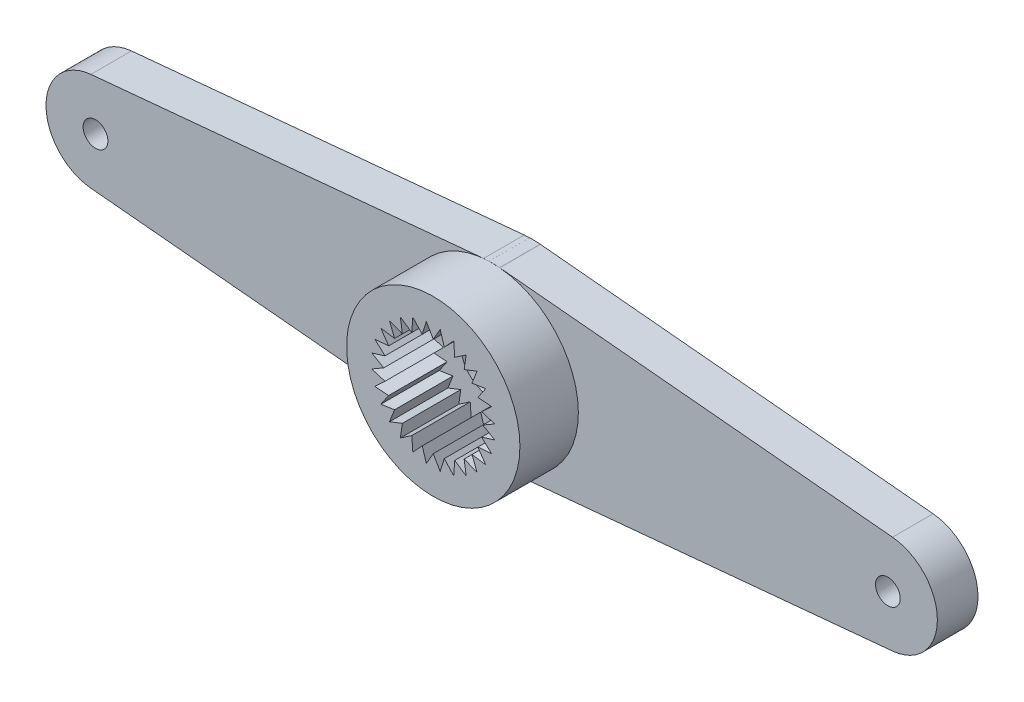
SolidWorks part; units mm, degrees
ref_plane "前视基准面" through (0, 0, 0) normal (0, 0, 1) x (1, 0, 0)
ref_plane "上视基准面" through (0, 0, 0) normal (0, 1, 0) x (1, 0, 0)
ref_plane "右视基准面" through (0, 0, 0) normal (1, 0, 0) x (0, 0, -1)
sketch "草图1" plane through (0, 0, 0) normal (0, 0, 1) x (1, 0, 0)
  circle A0 centre (0, 0) radius 1
extrude "凸台-拉伸1" add sketch "草图1" against normal blind 4.3
sketch "草图2" plane through (0, 0, 0) normal (0, 0, 1) x (1, 0, 0)
  circle A0 centre (0, 0) radius 2
extrude "凸台-拉伸2" add sketch "草图2" along normal blind 1
sketch "草图3" plane through (0, 0, 1) normal (0, 0, 1) x (1, 0, 0)
  line L0 (2.3597, -0.8257) -> (1.8019, -0.8678)
  line L29 (2.4843, -0.2799) -> (1.9499, -0.445)
  line L30 (2.4843, -0.2799) -> (2, 0)
  line L31 (2.3597, -0.8257) -> (1.9499, -0.445)
  line L32 (2.1168, -1.3301) -> (1.5637, -1.247)
  line L33 (2.1168, -1.3301) -> (1.8019, -0.8678)
  line L34 (1.7678, -1.7678) -> (1.247, -1.5637)
  line L35 (1.7678, -1.7678) -> (1.5637, -1.247)
  line L36 (1.3301, -2.1168) -> (0.8678, -1.8019)
  line L37 (1.3301, -2.1168) -> (1.247, -1.5637)
  line L38 (0.8257, -2.3597) -> (0.445, -1.9499)
  line L39 (0.8257, -2.3597) -> (0.8678, -1.8019)
  line L40 (0.2799, -2.4843) -> (0, -2)
  line L41 (0.2799, -2.4843) -> (0.445, -1.9499)
  line L42 (-0.2799, -2.4843) -> (-0.445, -1.9499)
  line L43 (-0.2799, -2.4843) -> (0, -2)
  line L44 (-0.8257, -2.3597) -> (-0.8678, -1.8019)
  line L45 (-0.8257, -2.3597) -> (-0.445, -1.9499)
  line L46 (-1.3301, -2.1168) -> (-1.247, -1.5637)
  line L47 (-1.3301, -2.1168) -> (-0.8678, -1.8019)
  line L48 (-1.7678, -1.7678) -> (-1.5637, -1.247)
  line L49 (-1.7678, -1.7678) -> (-1.247, -1.5637)
  line L50 (-2.1168, -1.3301) -> (-1.8019, -0.8678)
  line L51 (-2.1168, -1.3301) -> (-1.5637, -1.247)
  line L52 (-2.3597, -0.8257) -> (-1.9499, -0.445)
  line L53 (-2.3597, -0.8257) -> (-1.8019, -0.8678)
  line L54 (-2.4843, -0.2799) -> (-2, 0)
  line L55 (-2.4843, -0.2799) -> (-1.9499, -0.445)
  line L56 (-2.4843, 0.2799) -> (-1.9499, 0.445)
  line L57 (-2.4843, 0.2799) -> (-2, 0)
  line L58 (-2.3597, 0.8257) -> (-1.8019, 0.8678)
  line L59 (-2.3597, 0.8257) -> (-1.9499, 0.445)
  line L60 (-2.1168, 1.3301) -> (-1.5637, 1.247)
  line L61 (-2.1168, 1.3301) -> (-1.8019, 0.8678)
  line L62 (-1.7678, 1.7678) -> (-1.247, 1.5637)
  line L63 (-1.7678, 1.7678) -> (-1.5637, 1.247)
  line L64 (-1.3301, 2.1168) -> (-0.8678, 1.8019)
  line L65 (-1.3301, 2.1168) -> (-1.247, 1.5637)
  line L66 (-0.8257, 2.3597) -> (-0.445, 1.9499)
  line L67 (-0.8257, 2.3597) -> (-0.8678, 1.8019)
  line L68 (-0.2799, 2.4843) -> (0, 2)
  line L69 (-0.2799, 2.4843) -> (-0.445, 1.9499)
  line L70 (0.2799, 2.4843) -> (0.445, 1.9499)
  line L71 (0.2799, 2.4843) -> (0, 2)
  line L72 (0.8257, 2.3597) -> (0.8678, 1.8019)
  line L73 (0.8257, 2.3597) -> (0.445, 1.9499)
  line L74 (1.3301, 2.1168) -> (1.247, 1.5637)
  line L75 (1.3301, 2.1168) -> (0.8678, 1.8019)
  line L76 (1.7678, 1.7678) -> (1.5637, 1.247)
  line L77 (1.7678, 1.7678) -> (1.247, 1.5637)
  line L78 (2.1168, 1.3301) -> (1.8019, 0.8678)
  line L79 (2.1168, 1.3301) -> (1.5637, 1.247)
  line L80 (2.3597, 0.8257) -> (1.9499, 0.445)
  line L81 (2.3597, 0.8257) -> (1.8019, 0.8678)
  line L82 (2.4843, 0.2799) -> (2, 0)
  line L83 (2.4843, 0.2799) -> (1.9499, 0.445)
  arc A1 (0.445, -1.9499) -> (0.8678, -1.8019) centre (0, 0) ccw construction
  arc A2 (0, 2) -> (-0.445, 1.9499) centre (0, 0) ccw construction
  arc A3 (-1.5637, -1.247) -> (-1.247, -1.5637) centre (0, 0) ccw construction
  dimension "D1" = 28
extrude "凸台-拉伸3" add sketch "草图3" along normal blind 3.5
sketch "草图6" plane through (0, 0, 0) normal (0, 1, 0) x (1, 0, 0)
  line L0 (0, 0) -> (0, -4.5)
ref_plane "基准面3" through (0, 0, 4.5) normal (0, 0, 1) x (1, 0, 0)
sketch "草图7" plane through (0, 0, 4.5) normal (0, 0, 1) x (1, 0, 0)
  circle A0 centre (0, 0) radius 3.5
extrude "凸台-拉伸4" add sketch "草图7" against normal blind 4 separate body contours A0
combine bodies "组合1" operation type subtract main body 105 bodies to subtract 103
ref_plane "基准面5" through (0, 0, 0.5) normal (0, 0, -1) x (-1, 0, 0)
ref_point "点4"
sketch "草图9" plane through (0, 0, 0.5) normal (0, 0, -1) x (-1, 0, 0)
  line L2 (-16.1875, 1.9912) -> (-0.3281, 3.4846)
  line L3 (-16.1875, -1.9912) -> (-0.3281, -3.4846)
  line L5 (16.1875, -1.9912) -> (0.3281, -3.4846)
  line L6 (16.1875, 1.9912) -> (0.3281, 3.4846)
  arc A0 (-16.1875, 1.9912) -> (-16.1875, -1.9912) centre (-16, 0) ccw
  arc A1 (-0.3281, -3.4846) -> (0.3281, -3.4846) centre (0, 0) ccw
  arc A2 (16.1875, -1.9912) -> (16.1875, 1.9912) centre (16, 0) ccw
  arc A3 (0.3281, 3.4846) -> (-0.3281, 3.4846) centre (0, 0) ccw
  circle A4 centre (16, 0) radius 0.5
  circle A5 centre (-16, 0) radius 0.5
extrude "凸台-拉伸5" add sketch "草图9" against normal blind 1.64 separate body
hole_wizard "M2 六角凹头螺钉的柱形沉头孔1" positions "草图11" profile "草图12" counterbore size "M2" standard "ISO"
sketch "草图11" plane through (0, 0, 0.5) normal (0, 0, -1) x (-1, 0, 0)
  point P0 (0, 0)
sketch "草图12" plane through (0, 0, 0.5) normal (1, 0, 0) x (0, 1, 0)
  line L0 (0, 0) -> (0, 4)
  line L1 (0, 4) -> (1.25, 3.2489)
  line L2 (1.25, 3.2489) -> (1.25, 0.9)
  line L3 (1.25, 0.9) -> (2.4, 0.9)
  line L4 (2.4, 0.9) -> (2.4, 0)
  line L5 (2.4, 0) -> (0, 0)
  line L10 (0, 4) -> (-1.25, 3.2489) construction
  line L11 (0, -6.35) -> (0, 107.95) construction
  dimension "孔直径" = 2.5
  dimension "孔深度" = 4
  dimension "柱形沉头孔直径" = 4.8
  dimension "柱形沉头孔深度" = 0.9
  dimension "导头角度" = 118
